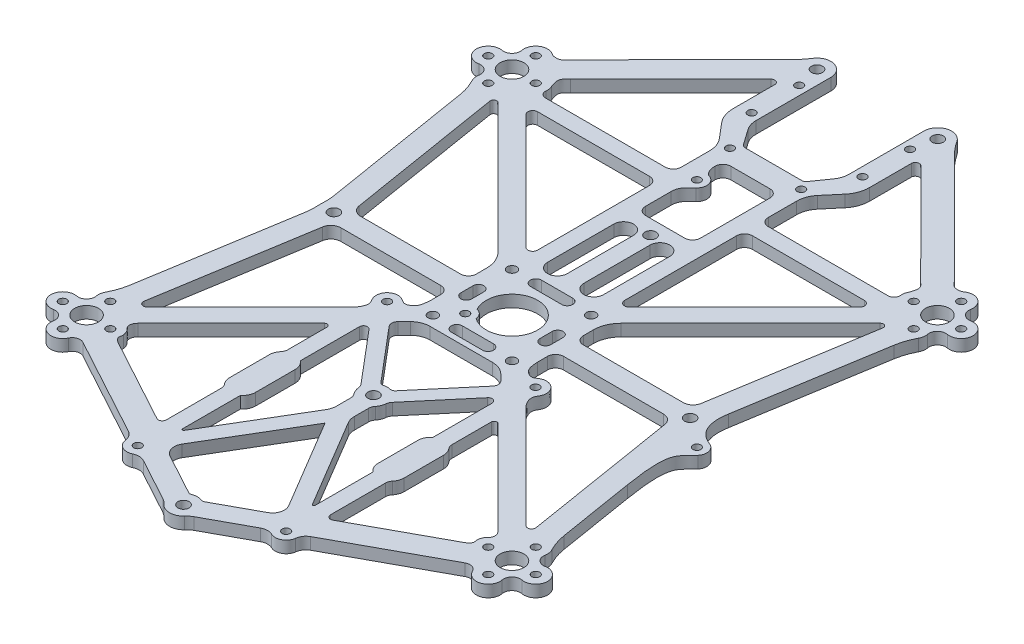
SolidWorks part; units mm, degrees
ref_plane "前视基准面" through (0, 0, 0) normal (0, 0, 1) x (1, 0, 0)
ref_plane "上视基准面" through (0, 0, 0) normal (0, 1, 0) x (1, 0, 0)
ref_plane "右视基准面" through (0, 0, 0) normal (1, 0, 0) x (0, 0, -1)
sketch "草图1" plane through (0, 0, 0) normal (0, 1, 0) x (1, 0, 0)
  line L0 (0, 0.5186) -> (0, -37.7018) construction
  line L1 (-53.9395, 0) -> (-21.7833, 0) construction
  line L2 (53.74, 59.74) -> (47.74, 53.74) construction
  line L3 (-10, 10) -> (10, 10) construction
  line L4 (-10, 10) -> (-10, -10) construction
  line L5 (-10, -10) -> (10, -10) construction
  line L6 (10, 10) -> (10, -10) construction
  line L7 (-10, 10) -> (10, -10) construction
  line L8 (-10, -10) -> (10, 10) construction
  line L9 (53.74, 59.74) -> (59.74, 53.74) construction
  line L10 (47.74, 53.74) -> (53.74, 47.74) construction
  line L11 (59.74, 53.74) -> (53.74, 47.74) construction
  line L12 (53.74, 59.74) -> (53.74, 47.74) construction
  line L13 (47.74, 53.74) -> (59.74, 53.74) construction
  line L14 (-15.25, 92.3) -> (-53.74, 53.74) construction
  line L15 (-53.74, -53.74) -> (0, -82.98) construction
  line L16 (-53.74, 53.74) -> (-45, 0) construction
  line L17 (-45, 0) -> (-53.74, -53.74) construction
  line L18 (53.74, -53.74) -> (0, -82.98) construction
  line L19 (-15.25, 92.3) -> (15.25, 92.3) construction
  line L20 (53.74, 53.74) -> (45, 0) construction
  line L21 (15.25, 92.3) -> (53.74, 53.74) construction
  line L22 (45, 0) -> (53.74, -53.74) construction
  line L23 (-54.8179, 41.6792) -> (-48.6469, 3.735)
  line L24 (-48.4964, 63.2397) -> (-20.7797, 91.0068)
  line L25 (-44.2499, 59.0009) -> (-18.9577, 84.339)
  line L28 (-49.6305, 44.0455) -> (-43.2151, 4.5987)
  line L29 (-54.8179, -41.6792) -> (-48.6469, -3.735)
  line L30 (-42.1559, 45.6915) -> (-13.0485, 16.5841)
  line L32 (-48.2752, 44.7397) -> (-15.5503, 12.0147)
  line L34 (-40.7475, 2.5) -> (-15.5, 2.5)
  line L36 (-40.7475, -2.5) -> (-15.5, -2.5)
  line L37 (-48.2778, -60.1273) -> (-3.0174, -84.7536) construction
  line L38 (-43.2151, -4.5987) -> (-49.531, -43.4337)
  line L39 (-17.25, 83.6325) -> (-17.25, 73.0731)
  line L40 (-11.75, 92.3) -> (-11.75, 73.3606)
  line L41 (-47.8368, -44.3013) -> (-15.5503, -12.0147) construction
  line L42 (13.5, 13.5) -> (-13.5, 13.5) construction
  line L43 (13.5, 13.5) -> (13.5, -13.5) construction
  line L44 (13.5, -13.5) -> (-13.5, -13.5) construction
  line L45 (-13.5, 13.5) -> (-13.5, -13.5) construction
  line L46 (13.5, 13.5) -> (-13.5, -13.5) construction
  line L47 (13.5, -13.5) -> (-13.5, 13.5) construction
  line L48 (-43.594, -55.8451) -> (-22.2279, -67.4704)
  line L49 (-45.456, -48.9915) -> (-21.945, -25.4805)
  line L50 (-13.5, 7.065) -> (-13.5, 4.5)
  line L51 (-13.5, -4.5) -> (-13.5, -7.065)
  line L52 (7.2144, 66.05) -> (-7.2144, 66.05)
  line L53 (-8.0335, 66.4764) -> (-10.8458, 70.4927)
  line L54 (-14, 86.55) -> (-14, 74.55) construction
  line L55 (-11, 60.9282) -> (-11, 53.74)
  line L56 (-15.5916, 68.5491) -> (-12.4215, 64.806)
  line L57 (-13, 51.74) -> (-43.2679, 51.74)
  line L58 (-41.3074, 47.74) -> (-13, 47.74)
  line L59 (-11, 45.74) -> (-11, 17.4326)
  line L60 (-21.8201, -18.2846) -> (-47.8368, -44.3013)
  line L61 (-18.75, -12.8) -> (18.75, -12.8) construction
  line L62 (-18.75, -12.8) -> (-18.75, -75.8) construction
  line L63 (-18.75, -75.8) -> (18.75, -75.8) construction
  line L64 (18.75, -12.8) -> (18.75, -75.8) construction
  line L65 (-18.75, -12.8) -> (18.75, -75.8) construction
  line L66 (-18.75, -75.8) -> (18.75, -12.8) construction
  line L67 (-20.75, -66.592) -> (-20.75, -25.9755) construction
  line L68 (-18.75, -39.3) -> (-18.75, -49.3) construction
  line L69 (-15.5, -39.3) -> (-15.5, -49.3) construction
  line L70 (-22, -39.3) -> (-22, -49.3) construction
  line L71 (-48.2778, -60.1273) -> (-23.023, -73.8685)
  line L72 (-14.8074, -78.3386) -> (-3.9568, -84.2424)
  line L73 (0, -44.3) -> (-18.75, -44.3) construction
  line L74 (-20.75, -25.9755) -> (-20.75, -35.8996)
  line L75 (-22, -39.3) -> (-22, -49.3)
  line L76 (-20.75, -52.7004) -> (-20.75, -66.592)
  line L77 (-18.75, -12.8) -> (0, -35) construction
  line L78 (-4.5906, 32.7859) -> (-4.5906, 16.0711) construction
  line L79 (-2.1025, 32.7859) -> (-2.1025, 16.0711)
  line L80 (-7.0787, 32.7859) -> (-7.0787, 16.0711)
  line L81 (-14.986, -21.131) -> (-3.9504, -34.1972)
  line L82 (-16.75, -21.7763) -> (-16.75, -36.7383)
  line L83 (7.9005, -12.8) -> (-7.9005, -12.8)
  line L84 (-11.436, -14.2645) -> (-12.9809, -15.8093)
  line L85 (-13.0719, -17.9731) -> (-1.8371, -31.2751)
  line L86 (-16.75, -51.8617) -> (-16.75, -66.4617)
  line L87 (-15.5, -39.3) -> (-15.5, -49.3)
  line L88 (-16.1922, -66.6152) -> (-2.8228, -44.1546)
  line L89 (-2.26, -38.4788) -> (-2.26, -42.1087)
  line L90 (0, -47.2326) -> (-13.4766, -69.8733)
  line L91 (-12.3325, -74.0429) -> (-1.9642, -79.6843)
  line L92 (4.5906, 32.7859) -> (4.5906, 16.0711) construction
  line L93 (2.1025, 32.7859) -> (2.1025, 16.0711)
  line L94 (7.0787, 32.7859) -> (7.0787, 16.0711)
  line L95 (16.75, -51.8617) -> (16.75, -66.4617)
  line L96 (15.5, -39.3) -> (15.5, -49.3)
  line L97 (16.75, -21.7763) -> (16.75, -36.7383)
  line L98 (14.986, -21.131) -> (3.9504, -34.1972)
  line L99 (2.26, -38.4788) -> (2.26, -42.1087)
  line L100 (16.1922, -66.6152) -> (2.8228, -44.1546)
  line L101 (22, -39.3) -> (22, -49.3)
  line L102 (20.75, -25.9755) -> (20.75, -35.8996)
  line L103 (45.456, -48.9915) -> (21.945, -25.4805)
  line L104 (43.594, -55.8451) -> (22.2279, -67.4704)
  line L105 (20.75, -52.7004) -> (20.75, -66.592)
  line L106 (13.5, -4.5) -> (13.5, -7.065)
  line L107 (40.7475, -2.5) -> (15.5, -2.5)
  line L108 (43.2151, -4.5987) -> (49.531, -43.4337)
  line L109 (21.8201, -18.2846) -> (47.8368, -44.3013)
  line L110 (48.2752, 44.7397) -> (15.5503, 12.0147)
  line L111 (49.6305, 44.0455) -> (43.2151, 4.5987)
  line L112 (40.7475, 2.5) -> (15.5, 2.5)
  line L113 (13.5, 7.065) -> (13.5, 4.5)
  line L114 (41.3074, 47.74) -> (13, 47.74)
  line L115 (11, 45.74) -> (11, 17.4326)
  line L116 (42.1559, 45.6915) -> (13.0485, 16.5841)
  line L117 (11, 60.9282) -> (11, 53.74)
  line L118 (15.5916, 68.5491) -> (12.4215, 64.806)
  line L119 (17.25, 83.6325) -> (17.25, 73.0731)
  line L120 (44.2499, 59.0009) -> (18.9577, 84.339)
  line L121 (13, 51.74) -> (43.2679, 51.74)
  line L122 (14.8074, -78.3386) -> (3.9568, -84.2424)
  line L123 (48.2778, -60.1273) -> (23.023, -73.8685)
  line L124 (54.8179, -41.6792) -> (48.6469, -3.735)
  line L125 (54.8179, 41.6792) -> (48.6469, 3.735)
  line L126 (48.4964, 63.2397) -> (20.7797, 91.0068)
  line L127 (11.75, 92.3) -> (11.75, 73.3606)
  line L128 (8.0335, 66.4764) -> (10.8458, 70.4927)
  line L129 (11.436, -14.2645) -> (12.9809, -15.8093)
  line L130 (13.0719, -17.9731) -> (1.8371, -31.2751)
  line L131 (0, -47.2326) -> (13.4766, -69.8733)
  line L132 (12.3325, -74.0429) -> (1.9642, -79.6843)
  line L133 (-10, 1.5391) -> (-10, -1.5391) construction
  line L134 (-4.9542, 60.225) -> (4.9542, 60.225)
  line L135 (-6.9542, 58.225) -> (-6.9542, 40.6642)
  line L136 (-4.9542, 38.6642) -> (4.9542, 38.6642)
  line L137 (6.9542, 58.225) -> (6.9542, 40.6642)
  line L138 (-6.9542, 60.225) -> (6.9542, 38.6642) construction
  line L139 (-6.9542, 38.6642) -> (6.9542, 60.225) construction
  line L140 (-8.6445, 1.5391) -> (-8.6445, -1.5391)
  line L141 (-11.3555, 1.5391) -> (-11.3555, -1.5391)
  line L142 (-3.9504, -10) -> (3.9504, -10) construction
  line L143 (-3.9504, -8.6094) -> (3.9504, -8.6094)
  line L144 (-3.9504, -11.3906) -> (3.9504, -11.3906)
  line L145 (-3.9504, 10) -> (3.9504, 10) construction
  line L146 (-3.9504, 8.6094) -> (3.9504, 8.6094)
  line L147 (-3.9504, 11.3906) -> (3.9504, 11.3906)
  line L148 (10, 1.5391) -> (10, -1.5391) construction
  line L149 (8.6445, 1.5391) -> (8.6445, -1.5391)
  line L150 (11.3555, 1.5391) -> (11.3555, -1.5391)
  circle A0 centre (53.74, 53.74) radius 3
  circle A2 centre (53.74, -53.74) radius 3
  circle A3 centre (-53.74, -53.74) radius 3
  circle A4 centre (-53.74, 53.74) radius 3
  circle A5 centre (15.25, 92.3) radius 1.4
  circle A6 centre (45, 0) radius 1.4
  circle A7 centre (0, -82.98) radius 1.4
  circle A8 centre (-45, 0) radius 1.4
  circle A9 centre (-15.25, 92.3) radius 1.4
  circle A10 centre (-10, 10) radius 1.2
  circle A11 centre (-10, -10) radius 1.2
  circle A12 centre (10, -10) radius 1.2
  circle A13 centre (10, 10) radius 1.2
  circle A14 centre (0, 0) radius 6.5
  circle A15 centre (53.74, 59.74) radius 1
  circle A16 centre (59.74, 53.74) radius 1
  circle A17 centre (53.74, 47.74) radius 1
  circle A18 centre (47.74, 53.74) radius 1
  circle A19 centre (53.74, 53.74) radius 6 construction
  circle A20 centre (-59.74, 53.74) radius 1
  circle A21 centre (-53.74, 47.74) radius 1
  circle A22 centre (-47.74, 53.74) radius 1
  circle A23 centre (-53.74, 59.74) radius 1
  circle A24 centre (59.74, -53.74) radius 1
  circle A25 centre (47.74, -53.74) radius 1
  circle A26 centre (53.74, -47.74) radius 1
  circle A27 centre (53.74, -59.74) radius 1
  circle A28 centre (-59.74, -53.74) radius 1
  circle A29 centre (-53.74, -47.74) radius 1
  circle A30 centre (-53.74, -59.74) radius 1
  circle A31 centre (-47.74, -53.74) radius 1
  arc A32 (-56.6876, 59.1819) -> (-51.9624, 62.1566) centre (-53.74, 59.74) cw
  arc A33 (-56.6876, 59.1819) -> (-59.1819, 56.6876) centre (-58.7848, 58.7848) cw
  arc A34 (-59.1819, 50.7924) -> (-59.1819, 56.6876) centre (-59.74, 53.74) cw
  arc A35 (-59.1819, -50.7924) -> (-59.1819, -56.6876) centre (-59.74, -53.74) ccw
  arc A36 (-59.1819, 50.7924) -> (-56.6876, 48.2981) centre (-58.7848, 48.6952) cw
  arc A37 (-45.0476, 55.0632) -> (-44.7586, 53.4067) centre (-47.74, 53.74) cw
  arc A38 (-56.6876, -59.1819) -> (-59.1819, -56.6876) centre (-58.7848, -58.7848) ccw
  arc A39 (-59.1819, -50.7924) -> (-56.6876, -48.2981) centre (-58.7848, -48.6952) ccw
  arc A40 (-56.6876, 48.2981) -> (-56.3872, 46.3286) centre (-53.74, 47.74) ccw
  arc A41 (-54.8179, 41.6792) -> (-56.3872, 46.3286) centre (-69.6234, 39.2714) ccw
  circle A42 centre (-45, 0) radius 3.5 construction
  arc A43 (-54.8179, -41.6792) -> (-56.3872, -46.3286) centre (-69.6234, -39.2714) cw
  arc A44 (-56.6876, -48.2981) -> (-56.3872, -46.3286) centre (-53.74, -47.74) cw
  arc A45 (-59.1819, -50.7924) -> (-56.6876, -48.2981) centre (-58.7848, -48.6952) ccw
  arc A46 (-48.491, 0.2511) -> (-48.491, -0.2511) centre (-45, 0) ccw
  arc A47 (-48.6469, -3.735) -> (-48.491, -0.2511) centre (-63.4523, -1.3271) ccw
  arc A48 (-48.6469, 3.735) -> (-48.491, 0.2511) centre (-63.4523, 1.3271) cw
  arc A49 (-43.2679, 51.74) -> (-44.7586, 53.4067) centre (-43.2679, 53.24) cw
  arc A50 (-49.6305, 44.0455) -> (-48.2752, 44.7397) centre (-48.8409, 44.174) cw
  arc A51 (-43.2151, 4.5987) -> (-40.7475, 2.5) centre (-40.7475, 5) ccw
  arc A52 (-56.6876, -59.1819) -> (-51.0287, -61.024) centre (-53.74, -59.74) ccw
  arc A53 (-51.0287, -61.024) -> (-48.2778, -60.1273) centre (-49.2293, -61.8761) cw
  arc A54 (-40.7475, -2.5) -> (-43.2151, -4.5987) centre (-40.7475, -5) ccw
  circle A55 centre (0, 35) radius 1.4
  circle A56 centre (0, -35) radius 1.4
  circle A57 centre (-15.25, 92.3) radius 3.5 construction
  arc A58 (-18.9577, 84.339) -> (-17.25, 83.6325) centre (-18.25, 83.6325) cw
  arc A59 (-18.1818, 94.2117) -> (-11.75, 92.3) centre (-15.25, 92.3) cw
  arc A60 (-20.7797, 91.0068) -> (-18.1818, 94.2117) centre (-34.9347, 105.136) ccw
  arc A61 (-49.531, -43.4337) -> (-47.8368, -44.3013) centre (-48.544, -43.5942) ccw
  arc A63 (-45.6594, -51.5788) -> (-44.7544, -53.4464) centre (-47.74, -53.74) cw
  arc A64 (-15.5503, -12.0147) -> (-13.5, -7.065) centre (-20.5, -7.065) ccw construction
  arc A65 (-15.5503, 12.0147) -> (-13.5, 7.065) centre (-20.5, 7.065) cw
  arc A66 (-15.5, -2.5) -> (-13.5, -4.5) centre (-15.5, -4.5) cw
  arc A67 (-15.5, 2.5) -> (-13.5, 4.5) centre (-15.5, 4.5) ccw
  circle A68 centre (0, -82.98) radius 3.5 construction
  circle A69 centre (-14, 86.55) radius 1
  circle A70 centre (-14, 74.55) radius 1
  circle A71 centre (-9, 64.05) radius 1
  arc A72 (-11.75, 73.3606) -> (-10.8458, 70.4927) centre (-6.75, 73.3606) ccw
  arc A73 (-7.2144, 66.05) -> (-8.0335, 66.4764) centre (-7.2144, 67.05) cw
  arc A74 (-17.25, 73.0731) -> (-15.5916, 68.5491) centre (-10.25, 73.0731) ccw
  arc A75 (-11, 60.9282) -> (-12.4215, 64.806) centre (-17, 60.9282) ccw
  arc A76 (-11, 53.74) -> (-13, 51.74) centre (-13, 53.74) cw
  arc A77 (-13, 47.74) -> (-11, 45.74) centre (-13, 45.74) cw
  arc A78 (-13.0485, 16.5841) -> (-11, 17.4326) centre (-12.2, 17.4326) ccw
  arc A79 (-42.1559, 45.6915) -> (-41.3074, 47.74) centre (-41.3074, 46.54) cw
  circle A80 centre (-18.75, -12.8) radius 1
  circle A81 centre (18.75, -12.8) radius 1
  circle A82 centre (-18.75, -75.8) radius 1
  circle A83 centre (18.75, -75.8) radius 1
  circle A84 centre (-18.75, -12.8) radius 2.75 construction
  arc A85 (-15.5, -39.3) -> (-22, -39.3) centre (-18.75, -39.3) ccw construction
  arc A86 (-22, -49.3) -> (-15.5, -49.3) centre (-18.75, -49.3) ccw construction
  circle A87 centre (-18.75, -75.8) radius 2.75 construction
  arc A88 (-21.4793, -76.1365) -> (-17.5501, -78.2744) centre (-18.75, -75.8) ccw
  arc A89 (-17.5501, -78.2744) -> (-14.8074, -78.3386) centre (-16.2412, -80.9738) cw
  arc A90 (-23.023, -73.8685) -> (-21.4793, -76.1365) centre (-24.4568, -76.5037) cw
  arc A91 (-22.2279, -67.4704) -> (-20.75, -66.592) centre (-21.75, -66.592) ccw
  arc A92 (-21.945, -25.4805) -> (-20.75, -25.9755) centre (-21.45, -25.9755) cw
  arc A93 (-21.2262, -37.195) -> (-22, -39.3) centre (-18.75, -39.3) ccw
  arc A94 (-22, -49.3) -> (-21.2262, -51.405) centre (-18.75, -49.3) ccw
  arc A95 (-20.75, -52.7004) -> (-21.2262, -51.405) centre (-22.75, -52.7004) ccw
  arc A96 (-20.75, -35.8996) -> (-21.2262, -37.195) centre (-22.75, -35.8996) cw
  arc A97 (-2.1025, 32.7859) -> (-7.0787, 32.7859) centre (-4.5906, 32.7859) ccw
  arc A98 (-7.0787, 16.0711) -> (-2.1025, 16.0711) centre (-4.5906, 16.0711) ccw
  arc A99 (-14.986, -21.131) -> (-16.75, -21.7763) centre (-15.75, -21.7763) ccw
  circle A100 centre (0, -35) radius 3.5 construction
  arc A101 (-12.9809, -15.8093) -> (-13.0719, -17.9731) centre (-11.8495, -16.9407) ccw
  arc A102 (0.8347, -31.601) -> (-0.8347, -31.601) centre (0, -35) ccw
  arc A103 (-1.8371, -31.2751) -> (-0.8347, -31.601) centre (-1.0731, -30.6298) ccw
  arc A104 (-16.75, -36.7383) -> (-15.5, -39.3) centre (-18.75, -39.3) cw
  arc A105 (-16.75, -51.8617) -> (-15.5, -49.3) centre (-18.75, -49.3) ccw
  arc A106 (-3.4862, -35.3104) -> (-2.7109, -37.2138) centre (0, -35) ccw
  arc A107 (-16.75, -66.4617) -> (-16.1922, -66.6152) centre (-16.45, -66.4617) ccw
  arc A108 (-2.7109, -37.2138) -> (-2.26, -38.4788) centre (-4.26, -38.4788) cw
  arc A109 (-3.9504, -34.1972) -> (-3.4862, -35.3104) centre (-5.4783, -35.4877) cw
  arc A110 (-2.26, -42.1087) -> (-2.8228, -44.1546) centre (-6.26, -42.1087) cw
  arc A111 (-13.4766, -69.8733) -> (-12.3325, -74.0429) centre (-10.8987, -71.4077) ccw
  arc A112 (2.1025, 32.7859) -> (7.0787, 32.7859) centre (4.5906, 32.7859) cw
  arc A113 (7.0787, 16.0711) -> (2.1025, 16.0711) centre (4.5906, 16.0711) cw
  arc A114 (16.75, -51.8617) -> (15.5, -49.3) centre (18.75, -49.3) cw
  arc A115 (16.75, -36.7383) -> (15.5, -39.3) centre (18.75, -39.3) ccw
  arc A116 (14.986, -21.131) -> (16.75, -21.7763) centre (15.75, -21.7763) cw
  arc A117 (3.9504, -34.1972) -> (3.4862, -35.3104) centre (5.4783, -35.4877) ccw
  arc A118 (3.4862, -35.3104) -> (2.7109, -37.2138) centre (0, -35) cw
  arc A119 (2.7109, -37.2138) -> (2.26, -38.4788) centre (4.26, -38.4788) ccw
  arc A120 (16.75, -66.4617) -> (16.1922, -66.6152) centre (16.45, -66.4617) cw
  arc A121 (2.26, -42.1087) -> (2.8228, -44.1546) centre (6.26, -42.1087) ccw
  arc A122 (21.2262, -37.195) -> (22, -39.3) centre (18.75, -39.3) cw
  arc A123 (20.75, -35.8996) -> (21.2262, -37.195) centre (22.75, -35.8996) ccw
  arc A124 (21.945, -25.4805) -> (20.75, -25.9755) centre (21.45, -25.9755) ccw
  arc A125 (45.6594, -51.5788) -> (44.7544, -53.4464) centre (47.74, -53.74) ccw
  arc A126 (22.2279, -67.4704) -> (20.75, -66.592) centre (21.75, -66.592) cw
  arc A127 (20.75, -52.7004) -> (21.2262, -51.405) centre (22.75, -52.7004) cw
  arc A128 (22, -49.3) -> (21.2262, -51.405) centre (18.75, -49.3) cw
  arc A129 (15.5, -2.5) -> (13.5, -4.5) centre (15.5, -4.5) ccw
  arc A130 (40.7475, -2.5) -> (43.2151, -4.5987) centre (40.7475, -5) cw
  arc A131 (49.531, -43.4337) -> (47.8368, -44.3013) centre (48.544, -43.5942) cw
  arc A132 (49.6305, 44.0455) -> (48.2752, 44.7397) centre (48.8409, 44.174) ccw
  arc A133 (43.2151, 4.5987) -> (40.7475, 2.5) centre (40.7475, 5) cw
  arc A134 (15.5503, 12.0147) -> (13.5, 7.065) centre (20.5, 7.065) ccw
  arc A135 (15.5, 2.5) -> (13.5, 4.5) centre (15.5, 4.5) cw
  arc A136 (13, 47.74) -> (11, 45.74) centre (13, 45.74) ccw
  arc A137 (13.0485, 16.5841) -> (11, 17.4326) centre (12.2, 17.4326) cw
  arc A138 (42.1559, 45.6915) -> (41.3074, 47.74) centre (41.3074, 46.54) ccw
  arc A139 (11, 60.9282) -> (12.4215, 64.806) centre (17, 60.9282) cw
  arc A140 (17.25, 73.0731) -> (15.5916, 68.5491) centre (10.25, 73.0731) cw
  arc A141 (18.9577, 84.339) -> (17.25, 83.6325) centre (18.25, 83.6325) ccw
  arc A142 (45.0476, 55.0632) -> (44.7586, 53.4067) centre (47.74, 53.74) ccw
  arc A143 (43.2679, 51.74) -> (44.7586, 53.4067) centre (43.2679, 53.24) ccw
  arc A144 (11, 53.74) -> (13, 51.74) centre (13, 53.74) ccw
  arc A145 (17.5501, -78.2744) -> (14.8074, -78.3386) centre (16.2412, -80.9738) ccw
  arc A146 (21.4793, -76.1365) -> (17.5501, -78.2744) centre (18.75, -75.8) cw
  arc A147 (23.023, -73.8685) -> (21.4793, -76.1365) centre (24.4568, -76.5037) ccw
  arc A148 (51.0287, -61.024) -> (48.2778, -60.1273) centre (49.2293, -61.8761) ccw
  arc A149 (56.6876, -59.1819) -> (51.0287, -61.024) centre (53.74, -59.74) cw
  arc A150 (56.6876, -59.1819) -> (59.1819, -56.6876) centre (58.7848, -58.7848) cw
  arc A151 (59.1819, -50.7924) -> (59.1819, -56.6876) centre (59.74, -53.74) cw
  arc A152 (59.1819, -50.7924) -> (56.6876, -48.2981) centre (58.7848, -48.6952) cw
  arc A153 (56.6876, -48.2981) -> (56.3872, -46.3286) centre (53.74, -47.74) ccw
  arc A154 (54.8179, -41.6792) -> (56.3872, -46.3286) centre (69.6234, -39.2714) ccw
  arc A155 (48.6469, -3.735) -> (48.491, -0.2511) centre (63.4523, -1.3271) cw
  arc A156 (48.491, 0.2511) -> (48.491, -0.2511) centre (45, 0) cw
  arc A157 (48.6469, 3.735) -> (48.491, 0.2511) centre (63.4523, 1.3271) ccw
  arc A158 (56.6876, 48.2981) -> (56.3872, 46.3286) centre (53.74, 47.74) cw
  arc A159 (54.8179, 41.6792) -> (56.3872, 46.3286) centre (69.6234, 39.2714) cw
  arc A160 (59.1819, 50.7924) -> (56.6876, 48.2981) centre (58.7848, 48.6952) ccw
  arc A161 (59.1819, 50.7924) -> (59.1819, 56.6876) centre (59.74, 53.74) ccw
  arc A162 (56.6876, 59.1819) -> (59.1819, 56.6876) centre (58.7848, 58.7848) ccw
  arc A163 (56.6876, 59.1819) -> (51.9624, 62.1566) centre (53.74, 59.74) ccw
  arc A164 (20.7797, 91.0068) -> (18.1818, 94.2117) centre (34.9347, 105.136) cw
  arc A165 (18.1818, 94.2117) -> (11.75, 92.3) centre (15.25, 92.3) ccw
  arc A166 (11.75, 73.3606) -> (10.8458, 70.4927) centre (6.75, 73.3606) cw
  arc A167 (7.2144, 66.05) -> (8.0335, 66.4764) centre (7.2144, 67.05) ccw
  arc A168 (12.9809, -15.8093) -> (13.0719, -17.9731) centre (11.8495, -16.9407) cw
  arc A169 (1.8371, -31.2751) -> (0.8347, -31.601) centre (1.0731, -30.6298) cw
  arc A170 (13.4766, -69.8733) -> (12.3325, -74.0429) centre (10.8987, -71.4077) cw
  arc A171 (-1.2876, -79.7254) -> (1.2876, -79.7254) centre (0, -82.98) cw
  arc A172 (-2.6133, -85.3083) -> (2.6133, -85.3083) centre (0, -82.98) ccw
  arc A173 (-3.9568, -84.2424) -> (-2.6133, -85.3083) centre (-6.3465, -88.6344) cw
  arc A174 (3.9568, -84.2424) -> (2.6133, -85.3083) centre (6.3465, -88.6344) ccw
  arc A175 (-1.9642, -79.6843) -> (-1.2876, -79.7254) centre (-1.5819, -78.9815) ccw
  arc A176 (1.9642, -79.6843) -> (1.2876, -79.7254) centre (1.5819, -78.9815) cw
  arc A177 (-4.9542, 60.225) -> (-6.9542, 58.225) centre (-4.9542, 58.225) ccw
  arc A178 (-6.9542, 40.6642) -> (-4.9542, 38.6642) centre (-4.9542, 40.6642) ccw
  arc A179 (4.9542, 38.6642) -> (6.9542, 40.6642) centre (4.9542, 40.6642) ccw
  arc A180 (4.9542, 60.225) -> (6.9542, 58.225) centre (4.9542, 58.225) cw
  circle A181 centre (9, 64.05) radius 1
  circle A182 centre (14, 74.55) radius 1
  circle A183 centre (14, 86.55) radius 1
  arc A184 (-7.9005, -12.8) -> (-11.436, -14.2645) centre (-7.9005, -17.8) ccw
  arc A185 (11.436, -14.2645) -> (7.9005, -12.8) centre (7.9005, -17.8) ccw
  arc A186 (-8.6445, 1.5391) -> (-11.3555, 1.5391) centre (-10, 1.5391) ccw
  arc A187 (-11.3555, -1.5391) -> (-8.6445, -1.5391) centre (-10, -1.5391) ccw
  arc A188 (-3.9504, -8.6094) -> (-3.9504, -11.3906) centre (-3.9504, -10) ccw
  arc A189 (3.9504, -11.3906) -> (3.9504, -8.6094) centre (3.9504, -10) ccw
  arc A190 (-3.9504, 8.6094) -> (-3.9504, 11.3906) centre (-3.9504, 10) cw
  arc A191 (3.9504, 11.3906) -> (3.9504, 8.6094) centre (3.9504, 10) cw
  arc A192 (8.6445, 1.5391) -> (11.3555, 1.5391) centre (10, 1.5391) cw
  arc A193 (11.3555, -1.5391) -> (8.6445, -1.5391) centre (10, -1.5391) cw
  spline S0 degree 3 poles (-51.9624, 62.1566) (-51.697, 61.9614) (-50.9261, 61.8002) (-49.4946, 61.8801) (-48.8515, 62.8839) (-48.4964, 63.2397) knots 0 0 0 0 0.236574 0.582738 1 1 1 1
  spline S1 degree 3 poles (-45.456, -48.9915) (-45.9688, -49.5044) (-46.2318, -50.321) (-46.0977, -51.1567) (-45.6594, -51.5788) knots 0 0 0 0 0.55921 1 1 1 1
  spline S2 degree 3 poles (-44.2499, 59.0009) (-44.658, 58.5921) (-45.7383, 57.7977) (-45.4601, 56.2471) (-45.2118, 55.3974) (-45.0476, 55.0632) knots 0 0 0 0 0.43488 0.721834 1 1 1 1
  spline S3 degree 3 poles (-44.7544, -53.4464) (-44.7175, -53.8213) (-45.0546, -54.4539) (-44.4379, -55.3622) (-43.8218, -55.7212) (-43.594, -55.8451) knots 0 0 0 0 0.347316 0.678667 1 1 1 1
  spline S4 degree 3 poles (-13.5, -7.065) (-13.5, -7.5323) (-13.6298, -8.4805) (-13.9854, -10.1733) (-15.9442, -11.538) (-17.3451, -10.3274) (-18.9218, -9.8498) (-20.9141, -10.6053) (-21.6289, -12.4502) (-21.3373, -14.0413) (-20.5988, -14.9216) (-20.5393, -16.5807) (-21.3274, -17.7919) (-21.8201, -18.2846) knots 0 0 0 0 0.081237 0.151161 0.290886 0.364497 0.432696 0.558641 0.672327 0.727732 0.821152 0.848566 1 1 1 1
  spline S5 degree 3 poles (45.456, -48.9915) (45.9688, -49.5044) (46.2318, -50.321) (46.0977, -51.1567) (45.6594, -51.5788) knots 0 0 0 0 0.55921 1 1 1 1
  spline S6 degree 3 poles (44.7544, -53.4464) (44.7175, -53.8213) (45.0546, -54.4539) (44.4379, -55.3622) (43.8218, -55.7212) (43.594, -55.8451) knots 0 0 0 0 0.347316 0.678667 1 1 1 1
  spline S7 degree 3 poles (13.5, -7.065) (13.5, -7.5323) (13.6298, -8.4805) (13.9854, -10.1733) (15.9442, -11.538) (17.3451, -10.3274) (18.9218, -9.8498) (20.9141, -10.6053) (21.6289, -12.4502) (21.3373, -14.0413) (20.5988, -14.9216) (20.5393, -16.5807) (21.3274, -17.7919) (21.8201, -18.2846) knots 0 0 0 0 0.081237 0.151161 0.290886 0.364497 0.432696 0.558641 0.672327 0.727732 0.821152 0.848566 1 1 1 1
  spline S8 degree 3 poles (44.2499, 59.0009) (44.658, 58.5921) (45.7383, 57.7977) (45.4601, 56.2471) (45.2118, 55.3974) (45.0476, 55.0632) knots 0 0 0 0 0.43488 0.721834 1 1 1 1
  spline S9 degree 3 poles (51.9624, 62.1566) (51.697, 61.9614) (50.9261, 61.8002) (49.4946, 61.8801) (48.8515, 62.8839) (48.4964, 63.2397) knots 0 0 0 0 0.236574 0.582738 1 1 1 1
  point P23 (0, 0)
  point P35 (53.74, 53.74)
  point P90 (-57.2755, 57.2755)
  point P94 (-57.2755, 50.2045)
  point P103 (-48.2505, -1.2978)
  point P108 (-55.3969, 45.239)
  point P115 (-48.2505, 1.2978)
  point P130 (-42.8737, 2.5)
  point P147 (-18.6468, 93.1435)
  point P165 (-13.5, -9.9645)
  point P170 (-13.5, 9.9645)
  point P173 (-13.5, -2.5)
  point P176 (-13.5, 2.5)
  point P190 (-11.75, 71.7841)
  point P193 (-7.735, 66.05)
  point P212 (0, -44.3)
  point P223 (-18.75, -44.3)
  point P242 (-16.5187, -77.4075)
  point P245 (-21.3116, -74.7997)
  point P260 (-20.75, -51.8617)
  point P263 (-20.75, -36.7383)
  point P266 (-4.5906, 24.4285)
  point P287 (-1.4003, -31.7923)
  point P301 (-2.26, -37.6725)
  point P304 (-3.4905, -34.7418)
  point P314 (4.5906, 24.4285)
  point P470 (0, 66.05)
  point P471 (0, -12.8)
  point P488 (3.0174, -84.7536)
  point P491 (-1.6144, -79.8746)
  point P494 (1.6144, -79.8746)
  point P495 (0, 49.4446)
  point P519 (-9.9716, -12.8)
  point P522 (9.9716, -12.8)
  point P525 (-10, 0)
  point P531 (0, -10)
  point P540 (0, 10)
  point P547 (10, 0)
  dimension "D3" = 6
  dimension "D4" = 2.8
  dimension "D9" = 2.4
  dimension "D11" = 12
  dimension "D12" = 2
  dimension "D13" = 13
  dimension "D16" = 3
  dimension "D18" = 3
  dimension "D21" = 15
  dimension "D22" = 2.5
  dimension "D26" = 2.5
  dimension "D27" = 2.5
  dimension "D19" = 15
  dimension "D20" = 7
  dimension "D25" = 0.8
  dimension "D30" = 2.5
  dimension "D32" = 7
  dimension "D33" = 1
  dimension "D35" = 20
  dimension "D39" = 1
  dimension "D40" = 3
  dimension "D41" = 7
  dimension "D42" = 2
  dimension "D43" = 7
  dimension "D44" = 2
  dimension "D53" = 5
  dimension "D54" = 1
  dimension "D56" = 7
  dimension "D57" = 6
  dimension "D58" = 1.5
  dimension "D59" = 2
  dimension "D61" = 2
  dimension "D62" = 1.2
  dimension "D66" = 2
  dimension "D67" = 5.5
  dimension "D72" = 3
  dimension "D73" = 1
  dimension "D74" = 0.7
  dimension "D75" = 2
  dimension "D78" = 1
  dimension "D79" = 7
  dimension "D81" = 1.6
  dimension "D83" = 1
  dimension "D85" = 0.3
  dimension "D86" = 2
  dimension "D87" = 2
  dimension "D88" = 4
  dimension "D90" = 3
  dimension "D91" = 5
  dimension "D92" = 0.8
  dimension "D93" = 2
  dimension "D94" = 5
  dimension "D1" = 107.48
  dimension "D2" = 107.48
  dimension "D5" = 15.25
  dimension "D6" = 45
  dimension "D7" = 92.3
  dimension "D8" = 82.98
  dimension "D10" = 20
  dimension "D14" = 3
  dimension "D15" = 6
  dimension "D17" = 5
  dimension "D23" = 2.5
  dimension "D24" = 2.5
  dimension "D28" = 3
  dimension "D29" = 2.5
  dimension "D31" = 35
  dimension "D34" = 2
  dimension "D36" = 27
  dimension "D37" = 2.5
  dimension "D38" = 2.5
  dimension "D45" = 12
  dimension "D46" = 14
  dimension "D47" = 5.75
  dimension "D48" = 10.5
  dimension "D49" = 9
  dimension "D50" = 125
  dimension "D51" = 2
  dimension "D52" = 7
  dimension "D55" = 11
  dimension "D60" = 4
  dimension "D63" = 6
  dimension "D64" = 37.5
  dimension "D65" = 63
  dimension "D68" = 2
  dimension "D69" = 6.5
  dimension "D70" = 10
  dimension "D71" = 10.3
  dimension "D76" = 2.5
  dimension "D77" = 2
  dimension "D80" = 2
  dimension "D82" = 1
  dimension "D84" = 2.5
  dimension "D89" = 1.5
extrude "凸台-拉伸1" add sketch "草图1" along normal blind 3 contours A163 S9 L126 A164 A165 L127 A166 L128 A167 L52 A73 L53 A72 L40 A59 A60 L24 S0 A32 A33 A34 A36 A40 A41 L23 A48 A46 A47 L29 A43 A44 A39 A35 A38 A52 A53 L71 A90 A88 A89 L72 A173 A172 A174 L122 A145 A146 A147 L123 A148 A149
sketch "草图3" plane through (0, 3, 0) normal (0, 1, 0) x (1, 0, 0)
  line L0 (-11, 60.9282) -> (-11, 53.74) construction
  line L1 (-6.25, 52.95) -> (52.25, 52.95) construction
  line L2 (-6.25, 52.95) -> (-6.25, -5.55) construction
  line L3 (-6.25, -5.55) -> (52.25, -5.55) construction
  line L4 (52.25, 52.95) -> (52.25, -5.55) construction
  line L5 (-6.25, 52.95) -> (52.25, -5.55) construction
  line L6 (-6.25, -5.55) -> (52.25, 52.95) construction
  line L7 (-13, 51.74) -> (-43.2679, 51.74) construction
  line L8 (54.8179, -41.6792) -> (48.6469, -3.735) construction
  line L9 (54.8179, 41.6792) -> (48.6469, 3.735) construction
  line L10 (51.7041, -22.5333) -> (49.2729, -22.5333)
  line L11 (49.2729, -22.5333) -> (47.9164, -14.5077)
  line L12 (47.9164, -14.5077) -> (46.9609, -2.5866)
  line L13 (46.9609, -2.5866) -> (47.6758, 6.4035)
  line L14 (47.6758, 6.4035) -> (48.9692, 5.7173)
  line L15 (-6.9542, 58.225) -> (-6.9542, 40.6642) construction
  line L16 (-6.9542, 47.162) -> (-8.9306, 47.162)
  line L17 (-8.9306, 47.162) -> (-9.5851, 54.2033)
  line L18 (-9.5851, 54.2033) -> (-7.9424, 59.4228)
  line L19 (-7.9424, 59.4228) -> (-6.9542, 58.225)
  circle A0 centre (52.25, -5.55) radius 1
  circle A1 centre (-6.25, -5.55) radius 1
  circle A2 centre (-6.25, 52.95) radius 1
  circle A3 centre (52.25, -5.55) radius 2.5 construction
  arc A4 (54.1737, -7.1466) -> (53.1119, -3.2033) centre (52.25, -5.55) ccw
  circle A5 centre (-6.25, -5.55) radius 2.5
  circle A6 centre (-6.25, 52.95) radius 2.5 construction
  arc A7 (-4.9542, 60.225) -> (-6.9542, 58.225) centre (-4.9542, 58.225) ccw construction
  arc A8 (-4.5721, 51.0967) -> (-5.4818, 55.3291) centre (-6.25, 52.95) ccw
  spline S0 degree 3 poles (51.7041, -22.5333) (49.5709, -9.4164) (51.7623, -10.0521) (54.1737, -7.1466) knots 0 0 0 0 1 1 1 1
  spline S1 degree 2 poles (53.1119, -3.2033) (47.8417, -1.2158) (48.9692, 5.7173) knots 0 0 0 1 1 1
  spline S2 degree 3 poles (-4.5721, 51.0967) (-5.8509, 49.9389) (-6.9542, 49.0901) (-6.9542, 47.162) knots 0 0 0 0 1 1 1 1
  spline S3 degree 3 poles (-5.4818, 55.3291) (-6.0009, 55.4967) (-6.703, 56.471) (-6.9542, 57.4937) (-6.9542, 58.225) knots 0 0 0 0 0.428204 1 1 1 1
  point P0 (23, 23.7)
  point P46 (51.3945, -11.1097)
  point P47 (53.8444, -7.4756)
  point P48 (52.1045, -9.3585)
  dimension "D4" = 2
  dimension "D5" = 5
  dimension "D6" = 5
  dimension "D7" = 5
  dimension "D1" = 58.5
  dimension "D2" = 4.75
  dimension "D3" = 1.21
extrude "机载电脑固定孔" add sketch "草图3" against normal blind 3
sketch "草图4" plane through (0, 3, 0) normal (0, 1, 0) x (1, 0, 0)
  circle A0 centre (-6.25, -5.55) radius 1
  arc A1 (-3.7625, -5.3003) -> (-5.708, -3.1095) centre (-6.25, -5.55) ccw construction
  circle A2 centre (-6.25, 52.95) radius 1
  dimension "D1" = 2
extrude "机载电脑固定" cut sketch "草图4" against normal blind 3
